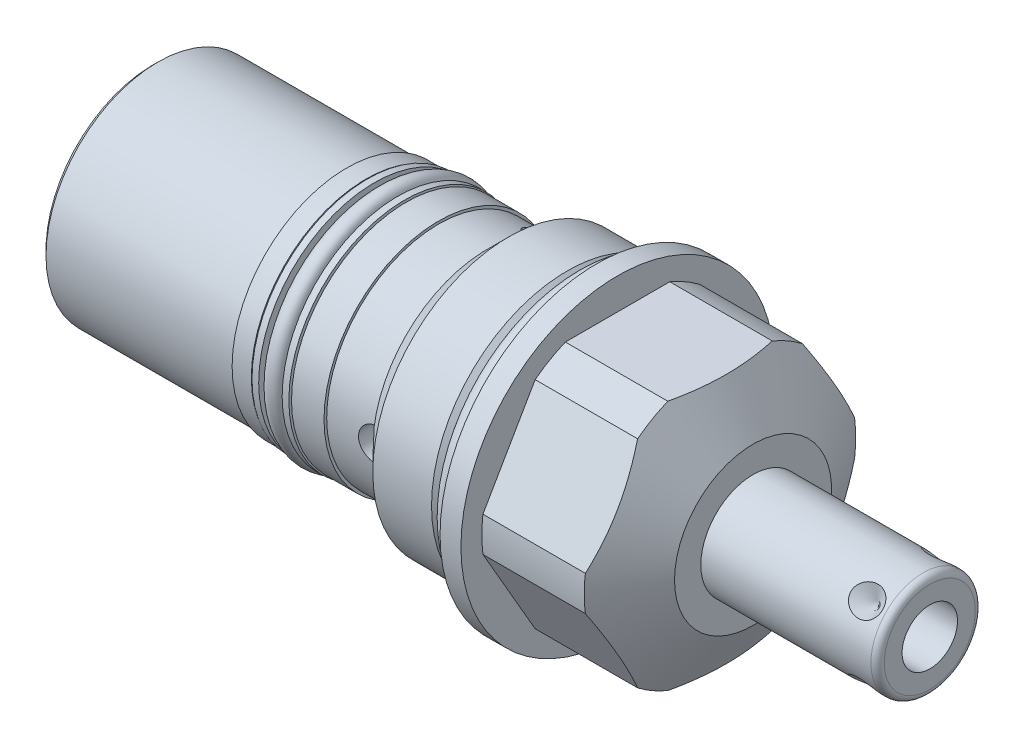
SolidWorks part; units mm, degrees
material "Alloy Steel"
ref_plane "Front Plane" through (0, 0, 0) normal (0, 0, 1) x (1, 0, 0)
ref_plane "Top Plane" through (0, 0, 0) normal (0, 1, 0) x (1, 0, 0)
ref_plane "Right Plane" through (0, 0, 0) normal (1, 0, 0) x (0, 0, -1)
ref_plane "Plane1" through (0, 0, 0) normal (1, 0, 0) x (0, 0, -1)
sketch "Sketch1" plane through (0, 0, 0) normal (1, 0, 0) x (0, 0, -1)
  circle A0 centre (0, 0) radius 23.8125
  dimension "D1" = 47.625
extrude "Extrude1" add sketch "Sketch1" along normal blind 23.7744 and the other way blind 67.4624
ref_plane "Plane2" through (0, 0, 0) normal (1, 0, 0) x (0, 0, -1)
sketch "Sketch2" plane through (0, 0, 0) normal (1, 0, 0) x (0, 0, -1)
  circle A0 centre (0, 0) radius 20.6375
  circle A1 centre (0, 0) radius 23.8125 construction
  circle A2 centre (0, 0) radius 23.8125
  dimension "D1" = 41.275
extrude "Cut-Extrude1" cut sketch "Sketch2" against normal up to next
ref_plane "Plane3" through (0, 0, 0) normal (0, 0, 1) x (1, 0, 0)
sketch "Sketch3" plane through (0, 0, 0) normal (0, 0, 1) x (1, 0, 0)
  line L0 (16.9187, 23.8125) -> (23.7744, 11.938)
  line L1 (-8.1458, 0) -> (17.0188, 0) construction
  line L2 (23.7744, 11.938) -> (23.7744, 23.8125)
  line L3 (23.7744, 23.8125) -> (16.9187, 23.8125)
  line L4 (23.7744, 23.8125) -> (0, 23.8125) construction
  dimension "D1" = 23.876
  dimension "D2" = 30
revolve "Cut-Revolve1" cut sketch "Sketch3" angle 360 about L1
ref_plane "Plane5" through (3.175, 0, 0) normal (-1, 0, 0) x (0, 0, 1)
sketch "Sketch5" plane through (3.175, 0, 0) normal (-1, 0, 0) x (0, 0, 1)
  line L0 (-10.9985, 19.05) -> (10.9985, 19.05)
  line L1 (10.9985, 19.05) -> (21.997, 0)
  line L2 (21.997, 0) -> (10.9985, -19.05)
  line L3 (10.9985, -19.05) -> (-10.9985, -19.05)
  line L4 (-10.9985, -19.05) -> (-21.997, 0)
  line L5 (-21.997, 0) -> (-10.9985, 19.05)
  line L6 (0, 0) -> (18.7904, 0) construction
  line L7 (0, 0) -> (10.9985, 19.05) construction
  line L8 (0, 0) -> (-10.9985, 19.05) construction
  circle A0 centre (0, 0) radius 23.8125 construction
  circle A1 centre (0, 0) radius 23.8125
  dimension "D1" = 38.1
  dimension "D2" = 120
  dimension "D3" = 60
extrude "Cut-Extrude3" cut sketch "Sketch5" against normal up to next
ref_plane "Plane7" through (3.175, 0, 0) normal (-1, 0, 0) x (0, 0, 1)
sketch "Sketch7" plane through (3.175, 0, 0) normal (-1, 0, 0) x (0, 0, 1)
  circle A0 centre (0, 0) radius 20.6375
  circle A1 centre (0, 0) radius 23.8125 construction
  circle A2 centre (0, 0) radius 23.8125
  dimension "D1" = 41.275
extrude "Cut-Extrude5" cut sketch "Sketch7" against normal up to next
ref_plane "Plane9" through (0, 0, 0) normal (0, 0, 1) x (1, 0, 0)
sketch "Sketch9" plane through (0, 0, 0) normal (0, 0, 1) x (1, 0, 0)
  line L0 (0, 20.6375) -> (0, 19.1389)
  line L1 (0, 19.1389) -> (-2.9718, 19.1389)
  line L2 (-2.9718, 19.1389) -> (-4.4704, 20.6375)
  line L3 (-4.4206, 0) -> (0.2105, 0) construction
  line L4 (0, 20.6375) -> (-4.4704, 20.6375)
  line L5 (0, 20.6375) -> (-67.4624, 20.6375) construction
  line L6 (0, 23.8125) -> (0, -23.8125) construction
  dimension "D1" = 2.9718
  dimension "D2" = 45
  dimension "D3" = 38.2778
revolve "Cut-Revolve3" cut sketch "Sketch9" angle 360 about L3
ref_plane "Plane10" through (0, 0, 0) normal (0, 0, 1) x (1, 0, 0)
sketch "Sketch10" plane through (0, 0, 0) normal (0, 0, 1) x (1, 0, 0)
  line L0 (-13.3985, 20.6375) -> (-16.6116, 17.4244)
  line L1 (-16.6116, 17.4244) -> (-67.4624, 17.4244)
  line L2 (-55.947, 0) -> (-8.6516, 0) construction
  line L4 (-67.4624, 20.6375) -> (-67.4624, 17.4244)
  line L5 (-4.4704, 20.6375) -> (-4.4704, -20.6375) construction
  line L6 (-4.4704, 20.6375) -> (-67.4624, 20.6375) construction
  line L7 (-13.3985, 20.6375) -> (-67.4624, 20.6375)
  dimension "D1" = 34.8488
  dimension "D2" = 45
  dimension "D3" = 8.9281
revolve "Cut-Revolve4" cut sketch "Sketch10" angle 360 about L2
ref_plane "Plane12" through (0, 0, 0) normal (0, 0, 1) x (1, 0, 0)
sketch "Sketch12" plane through (0, 0, 0) normal (0, 0, 1) x (1, 0, 0)
  line L0 (-35.0774, 17.4244) -> (-35.0774, 15.3924)
  line L1 (-35.0774, 15.3924) -> (-28.9687, 15.3924)
  line L2 (-28.9687, 15.3924) -> (-28.9687, 17.4244)
  line L3 (-31.7506, 0) -> (-25.0311, 0) construction
  line L4 (-35.0774, 17.4244) -> (-28.9687, 17.4244)
  line L5 (-16.6116, 17.4244) -> (-67.4624, 17.4244) construction
  line L6 (-67.4624, 17.4244) -> (-67.4624, -17.4244) construction
  dimension "D1" = 6.1087
  dimension "D2" = 30.7848
  dimension "D3" = 32.385
revolve "Cut-Revolve6" cut sketch "Sketch12" angle 360 about L3
ref_plane "Plane14" through (0, 0, 0) normal (0, 0, 1) x (0, -1, 0)
sketch "Sketch14" plane through (0, 0, 0) normal (0, 0, 1) x (0, -1, 0)
  line L0 (17.4244, -67.4624) -> (17.018, -67.4624)
  line L1 (17.018, -67.4624) -> (17.018, -37.9984)
  line L2 (17.018, -37.9984) -> (17.4244, -37.9984)
  line L3 (17.4244, -37.9984) -> (17.4244, -67.4624)
  line L4 (17.4244, -16.6116) -> (17.018, -16.6116)
  line L5 (17.018, -16.6116) -> (17.018, -24.0284)
  line L6 (17.018, -24.0284) -> (17.4244, -24.0284)
  line L7 (17.4244, -24.0284) -> (17.4244, -16.6116)
  line L8 (0, -55.866) -> (0, -10.3518) construction
  line L9 (17.4244, -67.4624) -> (17.4244, -35.0774) construction
  line L10 (17.4244, -28.9687) -> (17.4244, -16.6116) construction
  line L11 (-17.4244, -67.4624) -> (17.4244, -67.4624) construction
  dimension "D1" = 13.97
  dimension "D2" = 34.036
  dimension "D3" = 29.464
  dimension "D4" = 7.4168
revolve "Cut-Revolve8" cut sketch "Sketch14" angle 360 about L8
ref_plane "Plane15" through (0, 0, 0) normal (0, 0, 1) x (0, -1, 0)
sketch "Sketch15" plane through (0, 0, 0) normal (0, 0, 1) x (0, -1, 0)
  line L0 (0, -3.0937) -> (0, 0.1473) construction
  line L1 (-23.8125, 0) -> (23.8125, 0) construction
  circle A0 centre (20.6375, -1.4986) radius 1.4986
  dimension "D1" = 2.9972
  dimension "D2" = 1.4986
  dimension "D3" = 41.275
revolve "Revolve1" add sketch "Sketch15" angle 360 about L0
ref_plane "Plane16" through (0, 0, 0) normal (0, 0, 1) x (0, -1, 0)
sketch "Sketch16" plane through (0, 0, 0) normal (0, 0, 1) x (0, -1, 0)
  line L0 (15.3924, -29.2227) -> (17.5768, -29.2227)
  line L1 (17.5768, -29.2227) -> (17.5768, -30.2387)
  line L2 (17.5768, -30.2387) -> (15.3924, -30.2387)
  line L3 (15.3924, -30.2387) -> (15.3924, -29.2227)
  line L4 (15.3924, -34.8234) -> (17.5768, -34.8234)
  line L5 (17.5768, -34.8234) -> (17.5768, -33.8074)
  line L6 (17.5768, -33.8074) -> (15.3924, -33.8074)
  line L7 (15.3924, -33.8074) -> (15.3924, -34.8234)
  line L8 (0, -31.4712) -> (0, -25.3105) construction
  line L9 (-17.4244, -28.9687) -> (17.4244, -28.9687) construction
  line L10 (17.4244, -35.0774) -> (-17.4244, -35.0774) construction
  line L11 (15.3924, -35.0774) -> (15.3924, -28.9687) construction
  dimension "D1" = 1.016
  dimension "D3" = 35.1536
  dimension "D4" = 0.254
  dimension "D5" = 0.254
revolve "Revolve2" add sketch "Sketch16" angle 360 about L8
ref_plane "Plane17" through (0, 0, 0) normal (0, 0, 1) x (0, -1, 0)
sketch "Sketch17" plane through (0, 0, 0) normal (0, 0, 1) x (0, -1, 0)
  line L0 (0, -31.7506) -> (0, -25.0311) construction
  line L1 (17.5768, -33.8074) -> (-17.5768, -33.8074) construction
  circle A0 centre (16.7005, -32.0231) radius 1.3081
  point P0 (9.8298, -25.3365)
  point P1 (9.8298, -31.4452)
  dimension "D1" = 2.6162
  dimension "D2" = 33.401
  dimension "D3" = 1.7843
revolve "Revolve3" add sketch "Sketch17" angle 360 about L0
ref_plane "Plane18" through (0, 0, 0) normal (0, 0, 1) x (0, -1, 0)
sketch "S2D0001" plane through (0, 0, 0) normal (0, 0, 1) x (0, -1, 0)
  line L0 (0, 23.7744) -> (-7.9375, 23.7744)
  line L1 (-7.9375, 23.7744) -> (-7.9375, 49.6316)
  line L2 (-6.9215, 50.6476) -> (0, 50.6476)
  line L3 (0, 50.6476) -> (0, 23.7744)
  line L4 (0, 7.2658) -> (0, 37.3443) construction
  line L5 (11.938, 23.7744) -> (-11.938, 23.7744) construction
  line L6 (-23.8125, 0) -> (23.8125, 0) construction
  arc A0 (-6.9215, 50.6476) -> (-7.9375, 49.6316) centre (-6.9215, 49.6316) ccw
  dimension "D2" = 1.016
  dimension "D1" = 15.875
  dimension "D3" = 50.6476
revolve "Revolve4" add sketch "S2D0001" angle 360 about L4
ref_plane "Plane19" through (36.322, -2.8067, 0) normal (0, 0, 1) x (0, -1, 0)
sketch "Sketch19" plane through (36.322, -2.8067, 0) normal (0, 0, 1) x (0, -1, 0)
  line L0 (1.4097, 14.3256) -> (1.4097, -0.9144)
  line L1 (1.4097, -0.9144) -> (-2.8067, -3.4479)
  line L2 (1.4097, 14.3256) -> (-2.8067, 14.3256)
  line L3 (-2.8067, 14.3256) -> (-2.8067, -3.4479)
  line L4 (-2.8067, -18.6227) -> (-2.8067, 0.5923) construction
  line L5 (4.1148, 14.3256) -> (-9.7282, 14.3256) construction
  dimension "D1" = 8.4328
  dimension "D2" = 15.24
  dimension "D3" = 59
revolve "Cut-Revolve9" cut sketch "Sketch19" angle 360 about L4
ref_plane "Plane20" through (32.3596, 0, -5.5562) normal (0, 1, 0) x (1, 0, 0)
ref_plane "Plane21" through (0, 0, 0) normal (0, 0.7071, -0.7071) x (-1, 0, 0)
sketch "S2D0002" plane through (32.3596, -3.9289, -3.9289) normal (0, 0.7071, -0.7071) x (1, 0, 0)
  line L0 (14.3256, 2.3813) -> (16.7386, 2.3813)
  line L1 (16.7386, 2.3813) -> (14.3256, -0.0317)
  line L2 (14.3256, 2.3813) -> (14.3256, -0.0317)
  line L3 (14.3256, -3.3652) -> (14.3256, 0.0794) construction
  line L4 (17.272, 2.3812) -> (-8.5852, 2.3812) construction
  line L5 (18.288, -12.4778) -> (18.288, 1.3653) construction
  dimension "D1" = 3.9624
  dimension "D2" = 45
  dimension "D3" = 4.826
revolve "Cut-Revolve10" cut sketch "S2D0002" angle 360 about L3
chamfer "Chamfer1" distance 0.762 angle 45 1 edges at (-67.4624, 0, 17.018)
sketch "Sketch23" plane through (0, 0, 0) normal (0, 0, 1) x (1, 0, 0)
  line L0 (-67.4624, 16.256) -> (-67.4624, -16.256) construction
  circle A0 centre (-16.6624, 0) radius 2.5273
  dimension "D1" = 5.0546
  dimension "D2" = 50.8
extrude "Cut-Extrude7" cut sketch "Sketch23" along normal through all
sketch "Sketch25" plane through (-67.4624, 0, 0) normal (-1, 0, 0) x (0, 0, 1)
  circle A0 centre (0, 0) radius 3.1369
  dimension "D1" = 6.2738
extrude "Cut-Extrude8" cut sketch "Sketch25" against normal blind 0.762
sketch "Sketch26" plane through (-67.4624, 0, 0) normal (-1, 0, 0) x (0, 0, 1)
  circle A0 centre (0, 0) radius 13.0302
extrude "Extrude2" add sketch "Sketch26" along normal blind 0.508
sketch "Sketch28" plane through (-67.9704, 0, 0) normal (-1, 0, 0) x (0, 0, 1)
  circle A0 centre (0, 0) radius 3.1369
extrude "Cut-Extrude9" cut sketch "Sketch28" against normal blind 0.508
pattern_circular "CirPattern2" count 3 over 360 about axis through (7.2658, 0, 0) along (-1, 0, 0) of "Cut-Extrude7"
pattern_circular "CirPattern3" count 4 over 360 about axis through (7.2658, 0, 0) along (-1, 0, 0) of "Cut-Revolve10"
